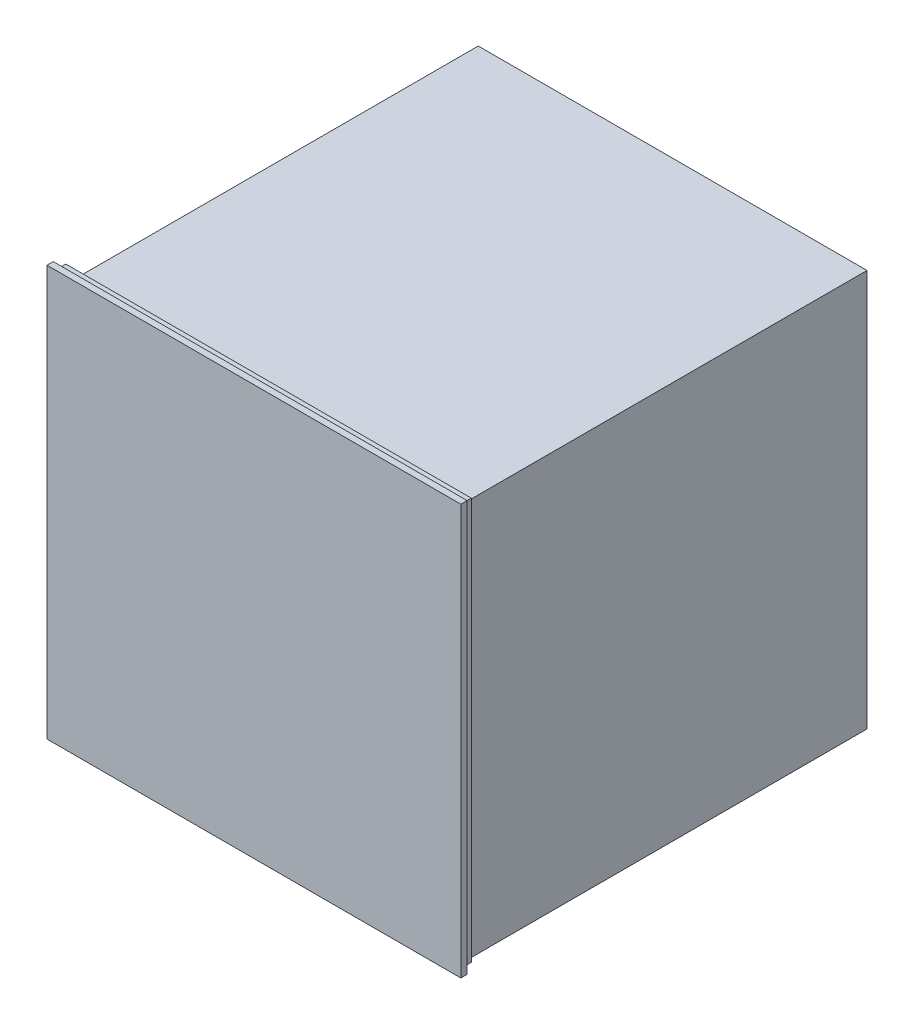
SolidWorks part; units mm, degrees
ref_plane "Спереди" through (0, 0, 0) normal (0, 0, 1) x (1, 0, 0)
ref_plane "Сверху" through (0, 0, 0) normal (0, 1, 0) x (1, 0, 0)
ref_plane "Справа" through (0, 0, 0) normal (1, 0, 0) x (0, 0, -1)
sketch "Эскиз1" plane through (0, 0, 0) normal (0, 0, 1) x (1, 0, 0)
  line L1 (-291, 288.5) -> (291, 288.5)
  line L2 (-291, 288.5) -> (-291, -288.5)
  line L3 (-291, -288.5) -> (291, -288.5)
  line L4 (291, 288.5) -> (291, -288.5)
  line L5 (-291, 288.5) -> (291, -288.5) construction
  line L6 (-291, -288.5) -> (291, 288.5) construction
  point P0 (0, 0)
extrude "Бобышка-Вытянуть1" add sketch "Эскиз1" along normal blind 12
sketch "Эскиз2" plane through (0, 0, 0) normal (0, 0, -1) x (-1, 0, 0)
  line L1 (-279, 275.5) -> (279, 275.5)
  line L2 (-279, 275.5) -> (-279, -294.5)
  line L3 (-279, -294.5) -> (279, -294.5)
  line L4 (279, 275.5) -> (279, -294.5)
extrude "Бобышка-Вытянуть2" add sketch "Эскиз2" along normal blind 580
sketch "Эскиз3" plane through (0, 0, 12) normal (0, 0, 1) x (1, 0, 0)
  line L1 (-297, 294.5) -> (297, 294.5)
  line L2 (-297, 294.5) -> (-297, -294.5)
  line L3 (-297, -294.5) -> (297, -294.5)
  line L4 (297, 294.5) -> (297, -294.5)
  line L5 (-297, 294.5) -> (297, -294.5) construction
  line L6 (-297, -294.5) -> (297, 294.5) construction
  point P0 (0, 0)
extrude "Бобышка-Вытянуть3" add sketch "Эскиз3" along normal blind 9
